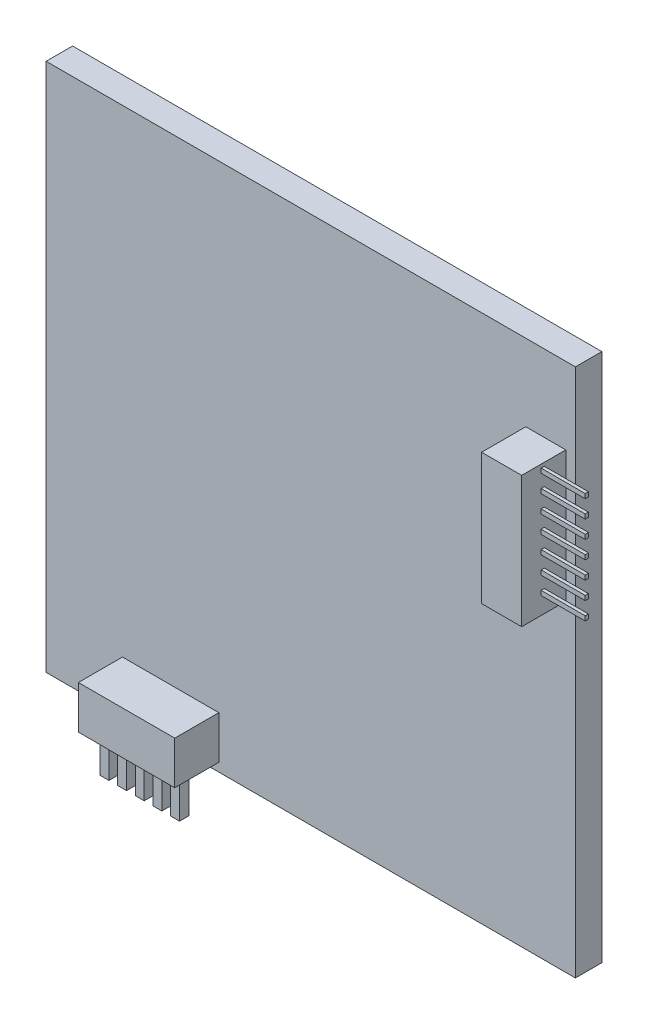
SolidWorks part; units mm, degrees
ref_plane "Front Plane" through (0, 0, 0) normal (0, 0, 1) x (1, 0, 0)
ref_plane "Top Plane" through (0, 0, 0) normal (0, 1, 0) x (1, 0, 0)
ref_plane "Right Plane" through (0, 0, 0) normal (1, 0, 0) x (0, 0, -1)
sketch "Sketch2" plane through (0, 0, 0) normal (0, 0, 1) x (1, 0, 0)
  line L1 (-29.434, 23.5613) -> (30.566, 23.5613)
  line L2 (-29.434, 23.5613) -> (-29.434, -36.4387)
  line L3 (-29.434, -36.4387) -> (30.566, -36.4387)
  line L4 (30.566, 23.5613) -> (30.566, -36.4387)
  dimension "D1" = 60
  dimension "D2" = 60
extrude "Boss-Extrude1" add sketch "Sketch2" along normal blind 3
sketch "Sketch3" plane through (0, 0, 3) normal (0, 0, 1) x (1, 0, 0)
  line L1 (-20.7796, -30.5996) -> (-9.8547, -30.5996)
  line L2 (-20.7796, -30.5996) -> (-20.7796, -35.4738)
  line L3 (-20.7796, -35.4738) -> (-9.8547, -35.4738)
  line L4 (-9.8547, -30.5996) -> (-9.8547, -35.4738)
  line L5 (24.9371, 14.865) -> (29.4751, 14.865)
  line L6 (24.9371, 14.865) -> (24.9371, 0)
  line L7 (24.9371, 0) -> (29.4751, 0)
  line L8 (29.4751, 14.865) -> (29.4751, 0)
extrude "Boss-Extrude2" add sketch "Sketch3" along normal blind 5
sketch "Sketch4" plane through (0, -35.4738, 0) normal (0, -1, 0) x (1, 0, 0)
  line L1 (-20.3054, 6.0111) -> (-19.3028, 6.0111)
  line L2 (-20.3054, 6.0111) -> (-20.3054, 4.9343)
  line L3 (-20.3054, 4.9343) -> (-19.3028, 4.9343)
  line L4 (-19.3028, 6.0111) -> (-19.3028, 4.9343)
extrude "Boss-Extrude3" add sketch "Sketch4" along normal blind 5
pattern_linear "LPattern1" count 5 spacing 2 along (1, 0, 0) of "Boss-Extrude3"
sketch "Sketch5" plane through (29.4751, 0, 0) normal (1, 0, 0) x (0, 0, -1)
  line L1 (-5.7978, 14.4774) -> (-5.4389, 14.4774)
  line L2 (-5.7978, 14.4774) -> (-5.7978, 13.9646)
  line L3 (-5.7978, 13.9646) -> (-5.4389, 13.9646)
  line L4 (-5.4389, 14.4774) -> (-5.4389, 13.9646)
extrude "Boss-Extrude4" add sketch "Sketch5" along normal blind 5
pattern_linear "LPattern2" count 7 spacing 2 along (0, -1, 0) of "Boss-Extrude4"
